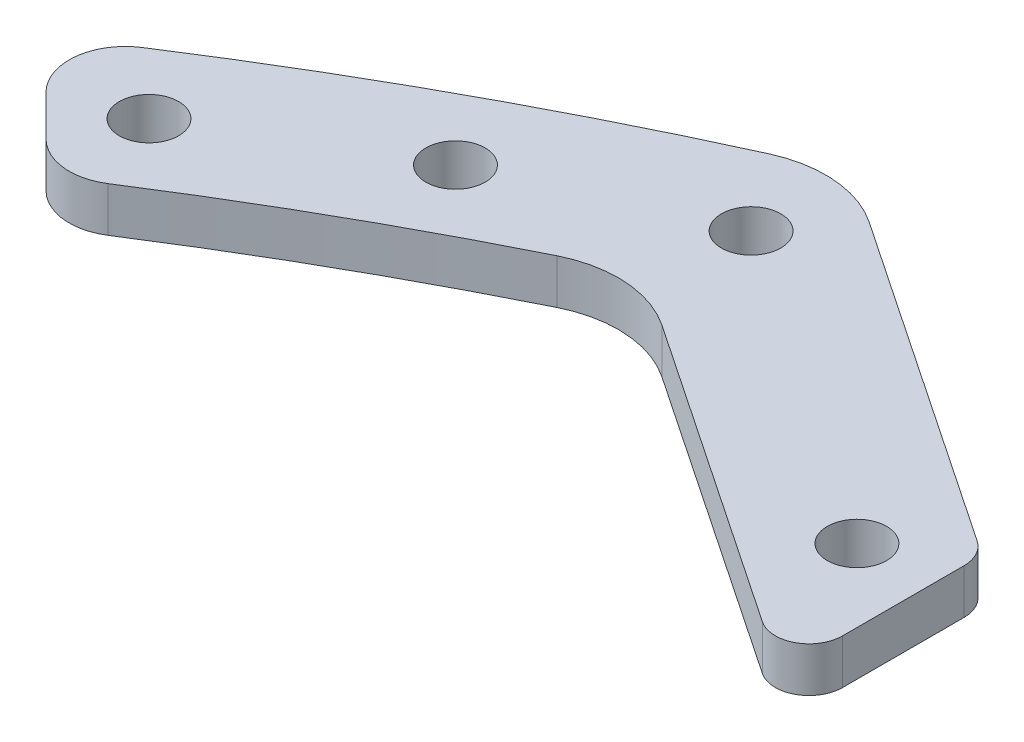
SolidWorks part; units mm, degrees
material "A-玻璃纤维"
ref_plane "前视基准面" through (0, 0, 0) normal (0, 0, 1) x (1, 0, 0)
ref_plane "上视基准面" through (0, 0, 0) normal (0, 1, 0) x (1, 0, 0)
ref_plane "右视基准面" through (0, 0, 0) normal (1, 0, 0) x (0, 0, -1)
sketch "草图1" plane through (0, 0, 0) normal (0, 1, 0) x (1, 0, 0)
  line L0 (0, 0) -> (275, 0) construction
  line L1 (0, 0) -> (0, 275) construction
  line L2 (0, 0) -> (194.4544, 194.4544) construction
  circle A0 centre (0, 0) radius 255
  circle A1 centre (0, 0) radius 275
  dimension "D1" = 510
  dimension "D2" = 20
  dimension "D3" = 45
extrude "凸台-拉伸1" add sketch "草图1" along normal blind 10
sketch "草图2" plane through (0, 10, 0) normal (0, 1, 0) x (1, 0, 0)
  line L0 (0, 0) -> (275, 0) construction
  line L1 (164.7559, 164.7559) -> (217.7889, 111.7229) construction
  line L2 (164.7559, 164.7559) -> (111.7229, 217.7889) construction
  line L3 (0, 0) -> (164.7559, 164.7559) construction
  line L4 (111.7229, 217.7889) -> (121.6224, 227.6884) construction
  line L5 (217.7889, 111.7229) -> (227.6884, 121.6224) construction
  line L6 (0, 0) -> (240.1716, 111.9938) construction
  line L7 (0, 0) -> (111.9938, 240.1716) construction
  line L8 (0, 0) -> (0, 275) construction
  line L9 (0, 185) -> (30, 185)
  line L10 (-110.5251, 257.2629) -> (-25.4233, 200)
  line L11 (111.9938, 240.1716) -> (30, 185)
  line L12 (0, 200) -> (-25.4233, 200)
  line L13 (240.1716, 111.9938) -> (185, 30)
  line L14 (185, 0) -> (185, 30)
  line L15 (-111.9938, 240.1716) -> (-30, 185)
  line L16 (0, 200) -> (25.4233, 200)
  line L17 (110.5251, 257.2629) -> (25.4233, 200)
  line L18 (257.2629, 110.5251) -> (200, 25.4233)
  line L19 (200, 0) -> (200, 25.4233)
  line L20 (0, 185) -> (-30, 185)
  line L21 (0, 185) -> (-30, 185) construction
  line L22 (0, 200) -> (-30, 200) construction
  line L23 (200, 0) -> (200, -1.5596) construction
  line L24 (185, 0) -> (185, -1.5596) construction
  line L25 (-200, -25.4233) -> (-200, 25.4233)
  line L26 (-257.2629, 110.5251) -> (-200, 25.4233)
  line L27 (-185, -30) -> (-185, 30)
  line L28 (-240.1716, 111.9938) -> (-185, 30)
  line L29 (185, 0) -> (185, -30)
  line L30 (200, 0) -> (200, -25.4233)
  line L31 (257.2629, -110.5251) -> (200, -25.4233)
  line L32 (240.1716, -111.9938) -> (185, -30)
  line L33 (164.7559, -164.7559) -> (111.7229, -217.7889) construction
  line L34 (110.5251, -257.2629) -> (25.4233, -200)
  line L35 (111.9938, -240.1716) -> (30, -185)
  line L36 (0, -185) -> (-30, -185)
  line L37 (0, -200) -> (-25.4233, -200)
  line L38 (0, -200) -> (25.4233, -200)
  line L39 (0, -185) -> (30, -185)
  line L40 (-111.9938, -240.1716) -> (-30, -185)
  line L41 (-110.5251, -257.2629) -> (-25.4233, -200)
  line L42 (-240.1716, -111.9938) -> (-185, -30)
  line L43 (-257.2629, -110.5251) -> (-200, -25.4233)
  circle A0 centre (0, 0) radius 275 construction
  arc A2 (111.9938, 240.1716) -> (240.1716, 111.9938) centre (0, 0) cw
  arc A3 (110.5251, 257.2629) -> (257.2629, 110.5251) centre (0, 0) cw
  arc A4 (-110.5251, 257.2629) -> (-257.2629, 110.5251) centre (0, 0) ccw
  arc A5 (-111.9938, 240.1716) -> (-240.1716, 111.9938) centre (0, 0) ccw
  arc A6 (110.5251, -257.2629) -> (257.2629, -110.5251) centre (0, 0) ccw
  arc A7 (111.9938, -240.1716) -> (240.1716, -111.9938) centre (0, 0) ccw
  arc A8 (-111.9938, -240.1716) -> (-240.1716, -111.9938) centre (0, 0) cw
  arc A9 (-110.5251, -257.2629) -> (-257.2629, -110.5251) centre (0, 0) cw
  point P60 (-185, 0)
  point P61 (-200, 0)
  dimension "D5" = 14
  dimension "D7" = 265
  dimension "D1" = 233
  dimension "D3" = 75
  dimension "D4" = 75
  dimension "D6" = 14
  dimension "D8" = 15
  dimension "D9" = 20
  dimension "D10" = 30
  dimension "D11" = 185
extrude "凸台-拉伸2" add sketch "草图2" along normal blind 10 separate body
sketch "草图8" plane through (0, 20, 0) normal (0, 1, 0) x (1, 0, 0)
  line L0 (0, 0) -> (-187.3833, 187.3833) construction
  line L1 (-243.7881, 137.7221) -> (-232.755, 126.689) construction
  line L2 (-137.7221, 243.7881) -> (-126.689, 232.755) construction
  line L3 (0, 0) -> (0, 200) construction
  line L4 (25.4233, 200) -> (-25.4233, 200) construction
  line L5 (-75, 233.3589) -> (-75, 215.2794) construction
  line L6 (75, 233.3589) -> (75, 215.2794) construction
  line L7 (-30, 185) -> (-111.9938, 240.1716) construction
  line L8 (-25.4233, 200) -> (-110.5251, 257.2629) construction
  line L9 (0, 0) -> (214.4019, 0) construction
  line L10 (200, -25.4233) -> (200, 25.4233) construction
  line L11 (-27.7116, 192.5) -> (-110.5251, 248.2231) construction
  line L12 (-10, 192.5) -> (-27.7116, 192.5) construction
  line L13 (-110.5251, 257.2629) -> (-110.5251, 248.2231) construction
  line L14 (-257.2629, 110.5251) -> (-248.2231, 110.5251) construction
  line L15 (-192.5, 27.7116) -> (-248.2231, 110.5251) construction
  line L16 (-233.3589, 75) -> (-215.2794, 75) construction
  line L17 (233.3589, 75) -> (215.2794, 75) construction
  line L18 (192.5, 27.7116) -> (248.2231, 110.5251) construction
  line L19 (257.2629, 110.5251) -> (248.2231, 110.5251) construction
  line L20 (243.7881, 137.7221) -> (232.755, 126.689) construction
  line L21 (137.7221, 243.7881) -> (126.689, 232.755) construction
  line L22 (0, 0) -> (187.3833, 187.3833) construction
  line L23 (110.5251, 257.2629) -> (110.5251, 248.2231) construction
  line L24 (27.7116, 192.5) -> (110.5251, 248.2231) construction
  line L25 (75, 233.3589) -> (75, 215.2794) construction
  arc A0 (-111.9938, 240.1716) -> (-240.1716, 111.9938) centre (0, 0) ccw construction
  arc A1 (-110.5251, 257.2629) -> (-257.2629, 110.5251) centre (0, 0) ccw construction
  circle A2 centre (-10, 192.5) radius 2.65
  circle A3 centre (10, 192.5) radius 2.65
  circle A4 centre (-10, -192.5) radius 2.65
  circle A5 centre (10, -192.5) radius 2.65
  circle A6 centre (192.5, 10) radius 2.65
  circle A8 centre (192.5, -10) radius 2.65
  circle A9 centre (-192.5, 10) radius 2.65
  circle A10 centre (-192.5, -10) radius 2.65
  circle A11 centre (-110.5251, 248.2231) radius 2.65
  circle A12 centre (-27.7116, 192.5) radius 2.65
  circle A13 centre (-44.3049, 203.6652) radius 2.65
  circle A14 centre (-56.7499, 212.0391) radius 2.65
  circle A15 centre (-69.1949, 220.413) radius 2.65
  circle A16 centre (-81.6399, 228.787) radius 2.65
  arc A17 (-238.2716, 132.2055) -> (-128.8116, 240.1233) centre (0, 0) cw construction
  circle A18 centre (-146.077, 230.0286) radius 2.65
  circle A19 centre (-164.4155, 217.2997) radius 2.65
  circle A20 centre (-183.6389, 201.3166) radius 2.65
  circle A21 centre (-201.3166, 183.6389) radius 2.65
  circle A22 centre (-217.2997, 164.4155) radius 2.65
  circle A23 centre (-230.0286, 146.077) radius 2.65
  circle A24 centre (-128.8116, 240.1233) radius 2.65
  circle A25 centre (-240.1233, 128.8116) radius 2.65
  circle A26 centre (-228.787, 81.6399) radius 2.65
  circle A27 centre (-220.413, 69.1949) radius 2.65
  circle A28 centre (-212.0391, 56.7499) radius 2.65
  circle A29 centre (-203.6652, 44.3049) radius 2.65
  circle A30 centre (-192.5, 27.7116) radius 2.65
  circle A31 centre (-248.2231, 110.5251) radius 2.65
  circle A32 centre (192.5, 27.7116) radius 2.65
  circle A33 centre (248.2231, 110.5251) radius 2.65
  circle A34 centre (203.6652, 44.3049) radius 2.65
  circle A35 centre (212.0391, 56.7499) radius 2.65
  circle A36 centre (220.413, 69.1949) radius 2.65
  circle A37 centre (228.787, 81.6399) radius 2.65
  circle A38 centre (240.1233, 128.8116) radius 2.65
  circle A39 centre (230.0286, 146.077) radius 2.65
  arc A40 (238.2716, 132.2055) -> (128.8116, 240.1233) centre (0, 0) ccw construction
  circle A41 centre (128.8116, 240.1233) radius 2.65
  circle A42 centre (201.3166, 183.6389) radius 2.65
  circle A43 centre (183.6389, 201.3166) radius 2.65
  circle A44 centre (164.4155, 217.2997) radius 2.65
  circle A45 centre (146.077, 230.0286) radius 2.65
  circle A46 centre (81.6399, 228.787) radius 2.65
  circle A47 centre (69.1949, 220.413) radius 2.65
  circle A48 centre (56.7499, 212.0391) radius 2.65
  circle A49 centre (44.3049, 203.6652) radius 2.65
  circle A50 centre (110.5251, 248.2231) radius 2.65
  circle A51 centre (27.7116, 192.5) radius 2.65
  circle A52 centre (217.2997, 164.4155) radius 2.65
  dimension "D1" = 75
  dimension "D3" = 5.3
  dimension "D4" = 20
  dimension "D5" = 7.5
  dimension "D6" = 5.3
  dimension "D7" = 20
  dimension "D8" = 7.5
  dimension "D10" = 5.3
  dimension "D11" = 5.3
  dimension "D12" = 15
  dimension "D13" = 15
  dimension "D14" = 15
  dimension "D15" = 20
  dimension "D16" = 5.3
  dimension "D17" = 20
  dimension "D18" = 25
  dimension "D19" = 20
  dimension "D20" = 25
  dimension "D21" = 25
  dimension "D22" = 5.3
  dimension "D23" = 20
  dimension "D2" = 75
  dimension "D9" = 7.5
extrude "切除-拉伸1" cut sketch "草图8" against normal through all
sketch "草图9" plane through (0, 20, 0) normal (0, 1, 0) x (1, 0, 0)
  line L0 (-157.0498, 231.8089) -> (-146.2376, 220.9968)
  line L1 (-64.1949, 226.0885) -> (-64.1949, 208.0089)
  line L2 (-25.4233, 200) -> (-110.5251, 257.2629) construction
  line L3 (-30, 185) -> (-111.9938, 240.1716) construction
  line L4 (-64.1949, 226.0885) -> (-110.5251, 257.2629)
  line L5 (-64.1949, 208.0089) -> (-111.9938, 240.1716)
  line L6 (0, 0) -> (0, 266.3831) construction
  line L7 (0, 0) -> (-187.3833, 187.3833) construction
  arc A0 (-110.5251, 257.2629) -> (-257.2629, 110.5251) centre (0, 0) ccw construction
  arc A1 (-111.9938, 240.1716) -> (-240.1716, 111.9938) centre (0, 0) ccw construction
  arc A2 (-110.5251, 257.2629) -> (-157.0498, 231.8089) centre (0, 0) ccw
  arc A3 (-111.9938, 240.1716) -> (-146.2376, 220.9968) centre (0, 0) ccw
  circle A4 centre (-69.1949, 220.413) radius 2.65 construction
  circle A5 centre (-146.077, 230.0286) radius 2.65 construction
  dimension "D1" = 5
  dimension "D2" = 6.5
extrude "切除-拉伸2" cut sketch "草图9" against normal through all flip side to cut
sketch "草图10" plane through (76.3367, 0, -113.4487) normal (-0.5583, 0, 0.8297) x (0.8297, 0, 0.5583)
  line L0 (-226.9958, 20) -> (-226.9958, 10) construction
  line L2 (-272.3229, 4) -> (-181.6687, 4)
  line L3 (-272.3229, 4) -> (-272.3229, 16)
  line L4 (-272.3229, 16) -> (-181.6687, 16)
  line L5 (-181.6687, 4) -> (-181.6687, 16)
  line L6 (-272.3229, 4) -> (-181.6687, 16) construction
  line L7 (-272.3229, 16) -> (-181.6687, 4) construction
  line L8 (-169.3835, 20) -> (-226.9958, 20) construction
  dimension "D1" = 4
extrude "切除-拉伸3" cut sketch "草图10" against normal through all both and the other way through all
fillet "圆角1" radius 3 1 edges at (-64.1949, 15, -208.0089)
fillet "圆角2" radius 10 2 edges at (-110.5251, 18, -257.2629) (-111.9938, 18, -240.1716)
fillet "圆角3" radius 5 3 edges at (-157.0498, 18, -231.8089) (-146.2376, 18, -220.9968) (-64.1949, 15, -226.0885)
sketch "草图11" plane through (76.3367, 0, -113.4487) normal (-0.5583, 0, 0.8297) x (0.8297, 0, 0.5583)
  line L1 (275, -10) -> (-275, -10)
  line L2 (275, -10) -> (275, 10)
  line L3 (275, 10) -> (-275, 10)
  line L4 (-275, -10) -> (-275, 10)
  line L5 (275, -10) -> (-275, 10) construction
  line L6 (275, 10) -> (-275, -10) construction
  point P0 (0, 0)
extrude "切除-拉伸4" cut sketch "草图11" against normal through all both and the other way through all
sketch "草图12" plane through (0, 20, 0) normal (0, 1, 0) x (1, 0, 0)
  line L0 (-75.1399, 233.4531) -> (-75.1399, 215.3735)
  line L1 (-66.4036, 227.5746) -> (-105.9495, 254.184) construction
  line L2 (-68.8697, 211.1544) -> (-107.2461, 236.9769) construction
  line L3 (-64.1949, 213.6434) -> (-64.1949, 223.4263) construction
  line L4 (-75.1399, 233.4531) -> (-60.7474, 233.4531)
  line L5 (-60.7474, 233.4531) -> (-60.7474, 205.6734)
  line L6 (-60.7474, 205.6734) -> (-74.8004, 205.6734)
  line L7 (-74.8004, 205.6734) -> (-75.1399, 215.3735)
  circle A0 centre (-81.6399, 228.787) radius 2.65 construction
  dimension "D1" = 6.5
extrude "切除-拉伸5" cut sketch "草图12" against normal through all
fillet "圆角4" radius 3 2 edges at (-75.1399, 18, -233.4531) (-75.1399, 18, -215.3735)
